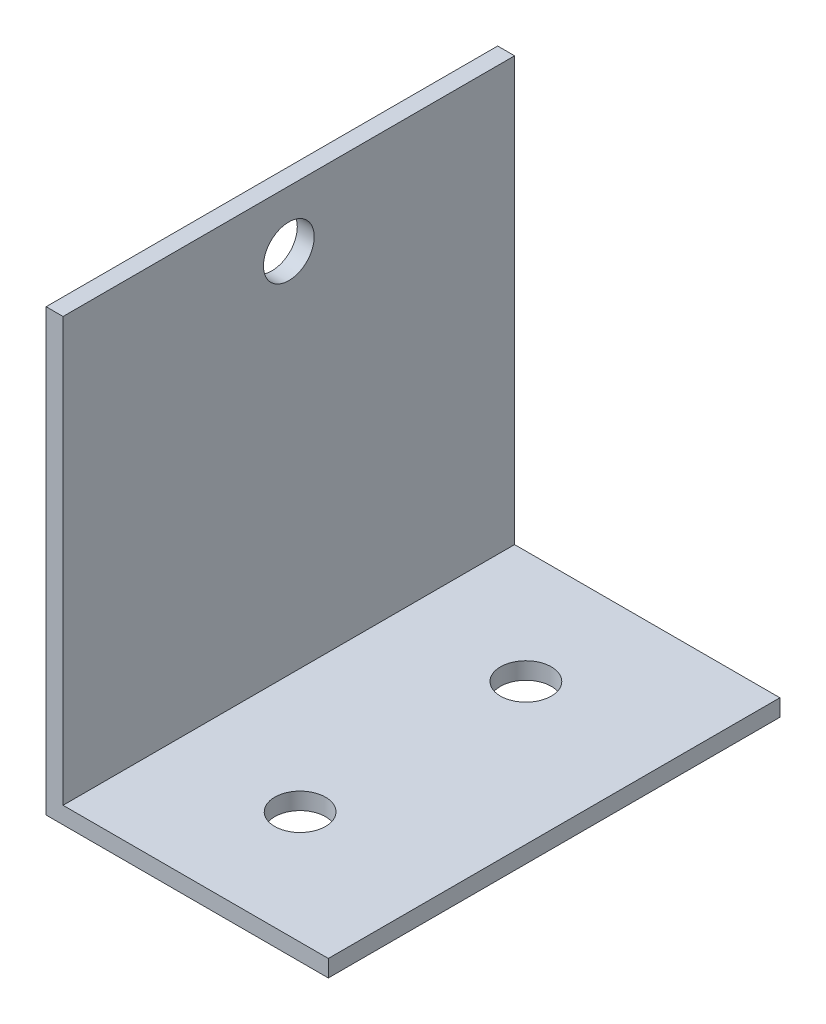
SolidWorks part; units mm, degrees
ref_plane "Plan de face" through (0, 0, 0) normal (0, 0, 1) x (1, 0, 0)
ref_plane "Plan de dessus" through (0, 0, 0) normal (0, 1, 0) x (1, 0, 0)
ref_plane "Plan de droite" through (0, 0, 0) normal (1, 0, 0) x (0, 0, -1)
sketch "Esquisse1" plane through (0, 0, 0) normal (0, 0, 1) x (1, 0, 0)
  line L0 (0, 0) -> (25, 0)
  line L1 (0, 0) -> (0, 39)
  dimension "D1" = 39
  dimension "D2" = 25
extrude "Extru.-Mince1" add sketch "Esquisse1" against normal blind 40 thin thin type one direction wall 1.5
sketch "Esquisse2" plane through (0, 1.5, 0) normal (0, 1, 0) x (-1, 0, 0)
  line L0 (-25, 0) -> (-1.5, 0) construction
  line L1 (-25, -40) -> (-1.5, -40) construction
  line L2 (-25, -40) -> (-25, 0) construction
  point P0 (-12.5, -10)
  point P2 (-12.5, -30)
  dimension "D1" = 10
  dimension "D2" = 10
  dimension "D4" = 12.5
  dimension "D6" = 12.5
hole_wizard "Dégagement M41" positions "Esquisse6" profile "Esquisse7" hole size "M4" standard "ISO" end condition through all
sketch "Esquisse6" plane through (0, 1.5, 0) normal (0, 1, 0) x (-1, 0, 0)
  point P1 (-12.5, -10)
  point P4 (-12.5, -30)
sketch "Esquisse7" plane through (12.5, 1.5, -10) normal (1, 0, 0) x (0, 0, 1)
  line L0 (0, 0) -> (0, 1.5)
  line L1 (0, 1.5) -> (2.25, 1.5)
  line L2 (2.25, 1.5) -> (2.25, 0)
  line L5 (2.25, 0) -> (0, 0)
  line L11 (0, -6.35) -> (0, 107.95) construction
  dimension "Diamètre du perçage jusqu'au prochain" = 4.5
  dimension "Profondeur du perçage jusqu'au prochain" = 1.5
sketch "Esquisse8" plane through (1.5, 0, 0) normal (1, 0, 0) x (0, 0, -1)
  line L0 (0, 1.5) -> (0, 39) construction
  line L2 (40, 39) -> (0, 39) construction
  point P0 (20, 34)
  dimension "D1" = 20
  dimension "D2" = 5
hole_wizard "Dégagement M42" positions "Esquisse10" profile "Esquisse9" hole size "M4" standard "ISO" end condition through all
sketch "Esquisse10" plane through (1.5, 0, 0) normal (1, 0, 0) x (0, 0, -1)
  point P1 (20, 34)
sketch "Esquisse9" plane through (1.5, 34, -20) normal (0, 1, 0) x (0, 0, -1)
  line L0 (0, 0) -> (0, 1.5)
  line L1 (0, 1.5) -> (2.25, 1.5)
  line L2 (2.25, 1.5) -> (2.25, 0)
  line L5 (2.25, 0) -> (0, 0)
  line L11 (0, -6.35) -> (0, 107.95) construction
  dimension "Diamètre du perçage jusqu'au prochain" = 4.5
  dimension "Profondeur du perçage jusqu'au prochain" = 1.5
